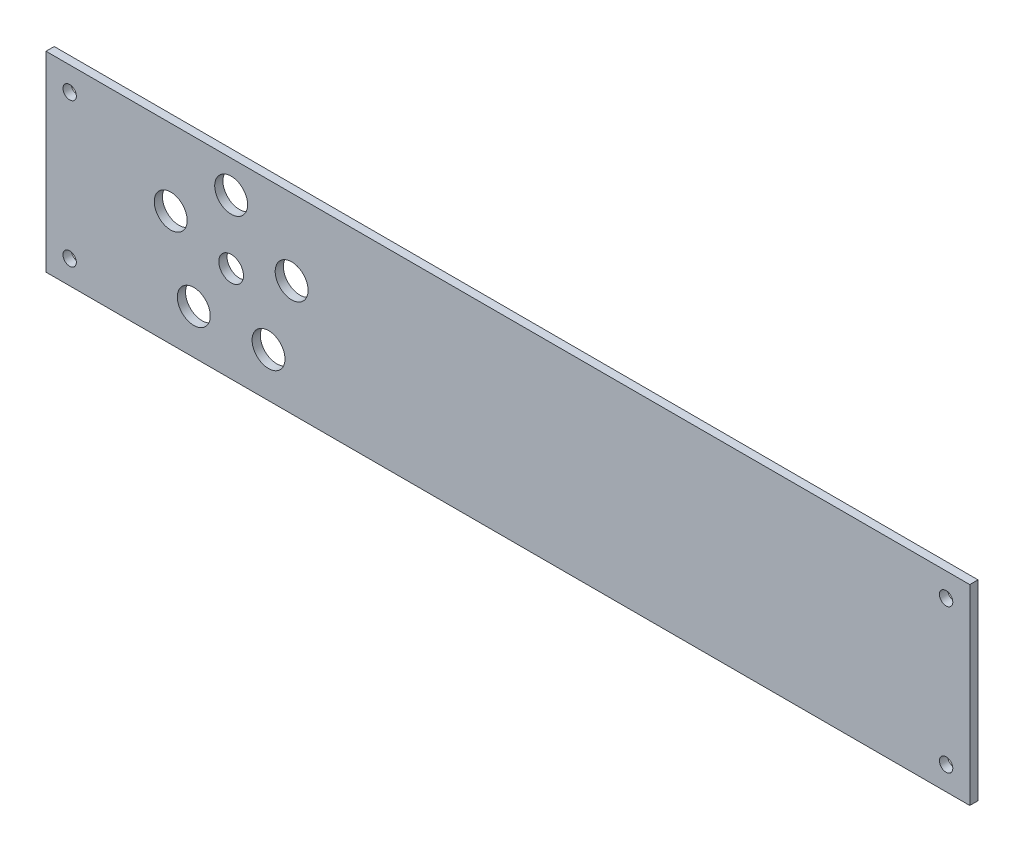
SolidWorks part; units mm, degrees
material "ABS PC"
ref_plane "Piano frontale" through (0, 0, 0) normal (0, 0, 1) x (1, 0, 0)
ref_plane "Piano superiore" through (0, 0, 0) normal (0, 1, 0) x (1, 0, 0)
ref_plane "Piano destro" through (0, 0, 0) normal (1, 0, 0) x (0, 0, -1)
sketch "Schizzo1" plane through (0, 0, 0) normal (0, 0, 1) x (1, 0, 0)
  line L0 (-449, 46.5) -> (0, 46.5) construction
  line L1 (0, 0) -> (-449, 0)
  line L2 (0, 0) -> (0, 93)
  line L3 (0, 93) -> (-449, 93)
  line L4 (-449, 0) -> (-449, 93)
  line L5 (-224.5, 93) -> (-224.5, 0) construction
  line L7 (-359, 77.4017) -> (-388.3893, 56.0492) construction
  line L8 (-359, 66.5) -> (-359, 26.5) construction
  line L9 (-388.3893, 56.0492) -> (-377.1636, 21.5) construction
  line L10 (-377.1636, 21.5) -> (-340.8364, 21.5) construction
  line L11 (-340.8364, 21.5) -> (-329.6107, 56.0492) construction
  line L12 (-329.6107, 56.0492) -> (-359, 77.4017) construction
  circle A0 centre (-388.3893, 56.0492) radius 8
  circle A1 centre (-437.5, 81.5) radius 3.25
  circle A2 centre (-11.5, 81.5) radius 3.25
  circle A3 centre (-11.5, 11.5) radius 3.25
  circle A4 centre (-437.5, 11.5) radius 3.25
  circle A5 centre (-359, 77.4017) radius 8
  circle A6 centre (-329.6107, 56.0492) radius 8
  circle A7 centre (-340.8364, 21.5) radius 8
  circle A8 centre (-377.1636, 21.5) radius 8
  circle A9 centre (-359, 46.5) radius 25 construction
  circle A16 centre (-359, 46.5) radius 6
  point P24 (-359, 46.5)
  dimension "D3" = 11.5
  dimension "D2" = 11.5
  dimension "D5" = 16
  dimension "D17" = 12
  dimension "D4" = 6.5
  dimension "D6" = 50
  dimension "D1" = 449
  dimension "D7" = 90
extrude "Estrusione-Estrusione1" add sketch "Schizzo1" along normal blind 4
